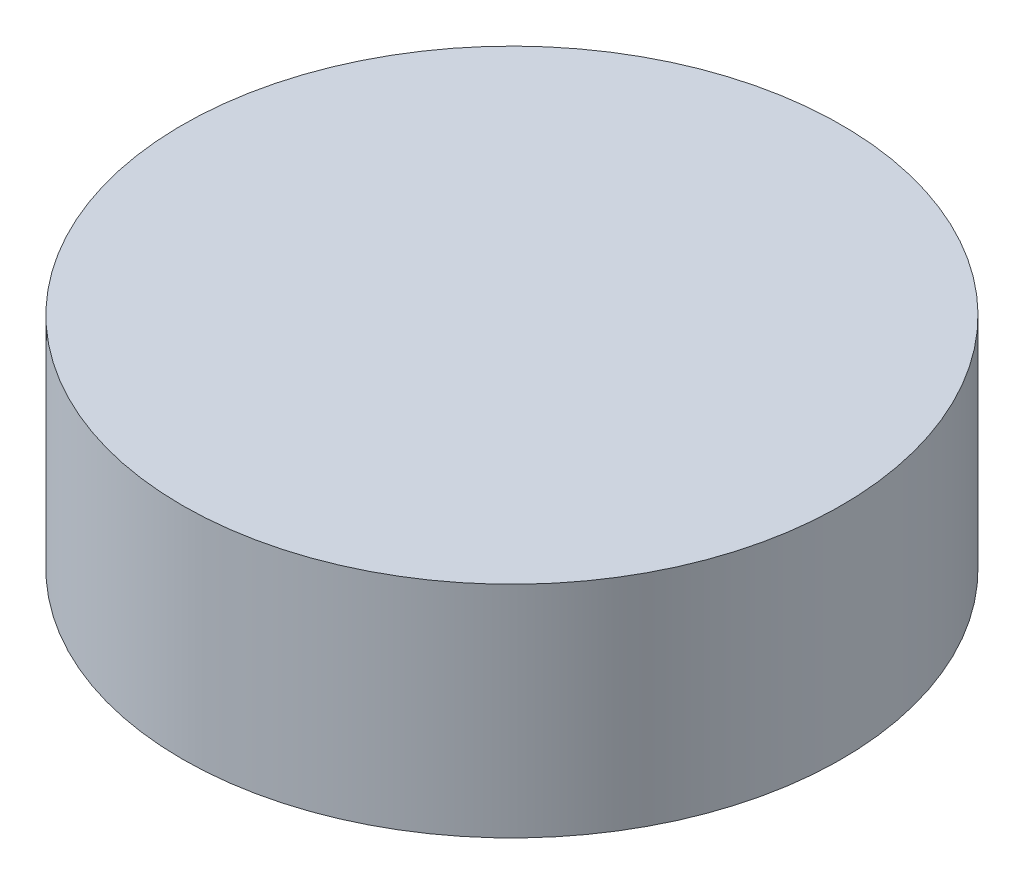
SolidWorks part; units mm, degrees
ref_plane "Front Plane" through (0, 0, 0) normal (0, 0, 1) x (1, 0, 0)
ref_plane "Top Plane" through (0, 0, 0) normal (0, 1, 0) x (1, 0, 0)
ref_plane "Right Plane" through (0, 0, 0) normal (1, 0, 0) x (0, 0, -1)
sketch "Sketch1" plane through (0, 0, 0) normal (0, 1, 0) x (1, 0, 0)
  circle A0 centre (0, 0) radius 1.5
  dimension "3" = 3
extrude "Boss-Extrude1" add sketch "Sketch1" along normal blind 1
